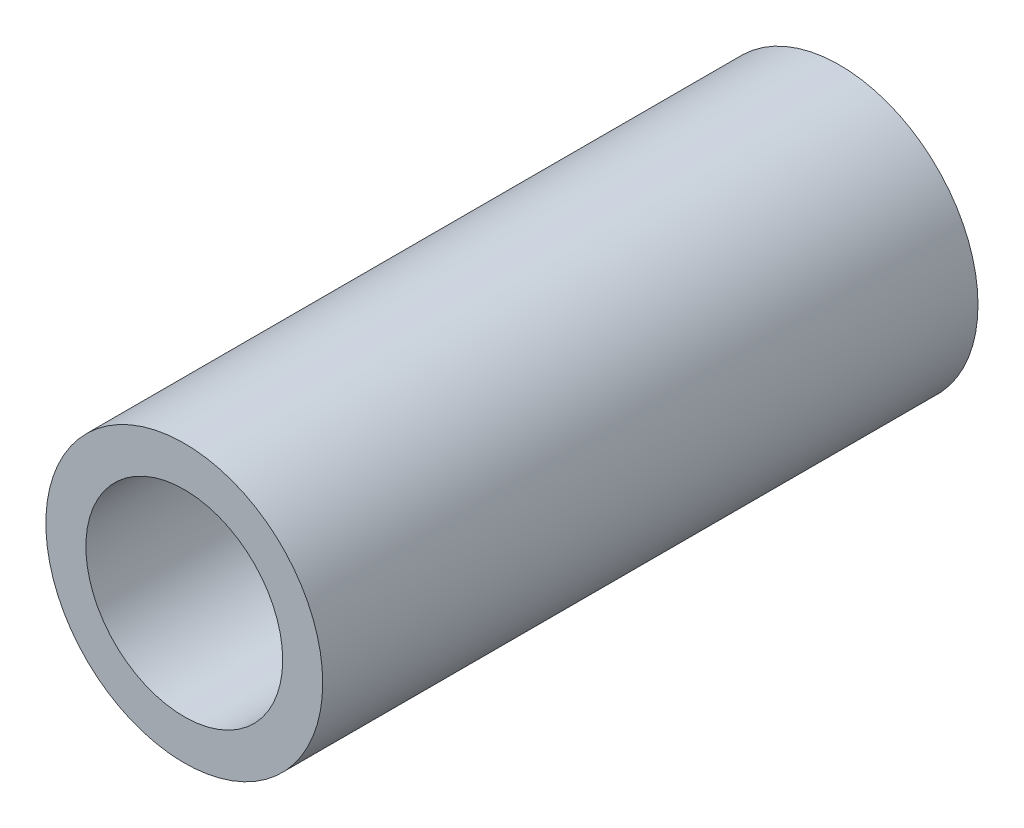
SolidWorks part; units mm, degrees
ref_plane "Front Plane" through (0, 0, 0) normal (0, 0, 1) x (1, 0, 0)
ref_plane "Top Plane" through (0, 0, 0) normal (0, 1, 0) x (1, 0, 0)
ref_plane "Right Plane" through (0, 0, 0) normal (1, 0, 0) x (0, 0, -1)
sketch "Sketch1" plane through (0, 0, 0) normal (0, 0, 1) x (1, 0, 0)
  circle A0 centre (0, 0) radius 10.3
  circle A1 centre (0, 0) radius 14.4875
  dimension "D1" = 20.6
  dimension "D2" = 28.975
extrude "Boss-Extrude1" add sketch "Sketch1" along normal blind 68.58
